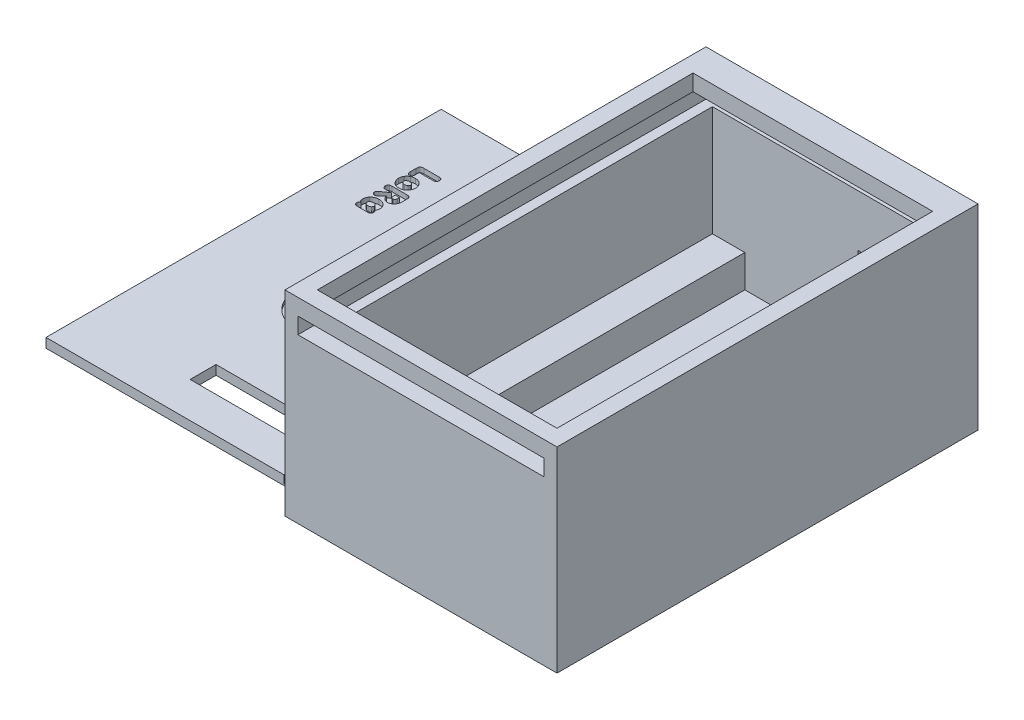
SolidWorks part; units mm, degrees
ref_plane "Plan de face" through (0, 0, 0) normal (0, 0, 1) x (1, 0, 0)
ref_plane "Plan de dessus" through (0, 0, 0) normal (0, 1, 0) x (1, 0, 0)
ref_plane "Plan de droite" through (0, 0, 0) normal (1, 0, 0) x (0, 0, -1)
sketch "Esquisse2" plane through (0, 0, 0) normal (0, 1, 0) x (1, 0, 0)
  line L1 (-71.4701, 44.7879) -> (-39.4701, 44.7879)
  line L2 (-71.4701, 44.7879) -> (-71.4701, -10.2121)
  line L3 (-71.4701, -10.2121) -> (-39.4701, -10.2121)
  line L4 (-39.4701, 44.7879) -> (-39.4701, -10.2121)
extrude "Boss.-Extru.1" add sketch "Esquisse2" along normal blind 3
sketch "Esquisse3" plane through (-71.4701, 0, 0) normal (-1, 0, 0) x (0, 0, 1)
  line L1 (-44.7879, 0) -> (10.2121, 0)
  line L2 (-44.7879, 0) -> (-44.7879, 30)
  line L3 (-44.7879, 30) -> (10.2121, 30)
  line L4 (10.2121, 0) -> (10.2121, 30)
extrude "Boss.-Extru.2" add sketch "Esquisse3" along normal blind 3
sketch "Esquisse5" plane through (-39.4701, 0, 0) normal (1, 0, 0) x (0, 0, -1)
  line L1 (-10.2121, 30) -> (44.7879, 30)
  line L2 (-10.2121, 30) -> (-10.2121, 0)
  line L3 (-10.2121, 0) -> (44.7879, 0)
  line L4 (44.7879, 30) -> (44.7879, 0)
extrude "Boss.-Extru.3" add sketch "Esquisse5" along normal blind 3
sketch "Esquisse6" plane through (0, 0, -44.7879) normal (0, 0, -1) x (-1, 0, 0)
  line L1 (36.4701, 30) -> (74.4701, 30)
  line L2 (36.4701, 30) -> (36.4701, 0)
  line L3 (36.4701, 0) -> (74.4701, 0)
  line L4 (74.4701, 30) -> (74.4701, 0)
extrude "Boss.-Extru.4" add sketch "Esquisse6" along normal blind 3
sketch "Esquisse7" plane through (0, 0, 10.2121) normal (0, 0, 1) x (1, 0, 0)
  line L1 (-74.4701, 30) -> (-36.4701, 30)
  line L2 (-74.4701, 30) -> (-74.4701, 0)
  line L3 (-74.4701, 0) -> (-36.4701, 0)
  line L4 (-36.4701, 30) -> (-36.4701, 0)
extrude "Boss.-Extru.5" add sketch "Esquisse7" along normal blind 3
sketch "Esquisse8" plane through (0, 3, 0) normal (0, 1, 0) x (1, 0, 0)
  line L0 (-39.4701, -10.2121) -> (-71.4701, -10.2121) construction
  line L1 (-71.4701, 44.7879) -> (-67.9701, 44.7879)
  line L2 (-71.4701, 44.7879) -> (-71.4701, -10.2121)
  line L3 (-71.4701, -10.2121) -> (-67.9701, -10.2121)
  line L4 (-67.9701, 44.7879) -> (-67.9701, -10.2121)
extrude "Boss.-Extru.6" add sketch "Esquisse8" along normal blind 5
sketch "Esquisse9" plane through (0, 3, 0) normal (0, 1, 0) x (1, 0, 0)
  line L0 (-67.9701, -10.2121) -> (-39.4701, -10.2121) construction
  line L1 (-39.4701, 44.7879) -> (-42.9701, 44.7879)
  line L2 (-39.4701, 44.7879) -> (-39.4701, -10.2121)
  line L3 (-39.4701, -10.2121) -> (-42.9701, -10.2121)
  line L4 (-42.9701, 44.7879) -> (-42.9701, -10.2121)
extrude "Boss.-Extru.7" add sketch "Esquisse9" along normal blind 5
sketch "Esquisse12" plane through (0, 0, 10.2121) normal (0, 0, -1) x (-1, 0, 0)
  line L0 (39.4701, 30) -> (39.4701, 8) construction
  line L1 (71.4701, 8) -> (71.4701, 30) construction
  line L2 (39.4701, 27.5) -> (71.4701, 27.5)
  line L3 (39.4701, 27.5) -> (39.4701, 25)
  line L4 (39.4701, 25) -> (71.4701, 25)
  line L5 (71.4701, 27.5) -> (71.4701, 25)
  point P0 (39.4701, 25)
  point P1 (39.4701, 27.5)
  dimension "D1" = 5
  dimension "D2" = 2.5
extrude "Enlèv. mat.-Extru.1" cut sketch "Esquisse12" against normal through all
sketch "Esquisse13" plane through (0, 0, -47.7879) normal (0, 0, -1) x (-1, 0, 0)
  line L1 (36.4701, 30) -> (74.4701, 30)
  line L2 (36.4701, 30) -> (36.4701, 0)
  line L3 (36.4701, 0) -> (74.4701, 0)
  line L4 (74.4701, 30) -> (74.4701, 0)
extrude "Boss.-Extru.8" add sketch "Esquisse13" along normal blind 2
sketch "Esquisse14" plane through (-36.4701, 0, 0) normal (1, 0, 0) x (0, 0, -1)
  line L1 (-13.2121, 30) -> (49.7879, 30)
  line L2 (-13.2121, 30) -> (-13.2121, 0)
  line L3 (-13.2121, 0) -> (49.7879, 0)
  line L4 (49.7879, 30) -> (49.7879, 0)
extrude "Boss.-Extru.9" add sketch "Esquisse14" along normal blind 2
sketch "Esquisse15" plane through (0, 0, 13.2121) normal (0, 0, 1) x (1, 0, 0)
  line L1 (-74.4701, 30) -> (-34.4701, 30)
  line L2 (-74.4701, 30) -> (-74.4701, 0)
  line L3 (-74.4701, 0) -> (-34.4701, 0)
  line L4 (-34.4701, 30) -> (-34.4701, 0)
extrude "Boss.-Extru.10" add sketch "Esquisse15" along normal blind 2
sketch "Esquisse16" plane through (0, 0, 13.2121) normal (0, 0, -1) x (-1, 0, 0)
  line L0 (71.4701, 25) -> (71.4701, 27.5) construction
  line L1 (39.4701, 25) -> (71.4701, 25)
  line L2 (39.4701, 25) -> (39.4701, 27.5)
  line L3 (39.4701, 27.5) -> (71.4701, 27.5)
  line L4 (71.4701, 25) -> (71.4701, 27.5)
extrude "Enlèv. mat.-Extru.2" cut sketch "Esquisse16" against normal blind 2
sketch "Esquisse17" plane through (-74.4701, 0, 0) normal (-1, 0, 0) x (0, 0, 1)
  line L1 (-49.7879, 30) -> (15.2121, 30)
  line L2 (-49.7879, 30) -> (-49.7879, 0)
  line L3 (-49.7879, 0) -> (15.2121, 0)
  line L4 (15.2121, 30) -> (15.2121, 0)
extrude "Boss.-Extru.11" add sketch "Esquisse17" along normal blind 2
sketch "Esquisse18" plane through (-39.4701, 0, 0) normal (-1, 0, 0) x (0, 0, 1)
  line L0 (-44.7879, 8) -> (-44.7879, 30) construction
  line L1 (15.2121, 27.5) -> (-44.7879, 27.5)
  line L2 (15.2121, 27.5) -> (15.2121, 25)
  line L3 (15.2121, 25) -> (-44.7879, 25)
  line L4 (-44.7879, 27.5) -> (-44.7879, 25)
extrude "Enlèv. mat.-Extru.3" cut sketch "Esquisse18" against normal blind 3
sketch "Esquisse19" plane through (-71.4701, 0, 0) normal (1, 0, 0) x (0, 0, -1)
  line L0 (44.7879, 30) -> (44.7879, 8) construction
  line L1 (-15.2121, 27.5) -> (44.7879, 27.5)
  line L2 (-15.2121, 27.5) -> (-15.2121, 25)
  line L3 (-15.2121, 25) -> (44.7879, 25)
  line L4 (44.7879, 27.5) -> (44.7879, 25)
extrude "Enlèv. mat.-Extru.4" cut sketch "Esquisse19" against normal blind 3
sketch "Esquisse20" plane through (0, 0, -44.7879) normal (0, 0, 1) x (1, 0, 0)
  line L1 (-74.4701, 27.5) -> (-36.4701, 27.5)
  line L2 (-74.4701, 27.5) -> (-74.4701, 25)
  line L3 (-74.4701, 25) -> (-36.4701, 25)
  line L4 (-36.4701, 27.5) -> (-36.4701, 25)
extrude "Enlèv. mat.-Extru.5" cut sketch "Esquisse20" against normal blind 3
sketch "Esquisse22" plane through (0, 0, 0) normal (0, -1, 0) x (1, 0, 0)
  line L1 (-76.4701, 15.2121) -> (-80.6146, 15.2121)
  line L2 (-76.4701, 15.2121) -> (-76.4701, -49.7879)
  line L3 (-76.4701, -49.7879) -> (-80.6146, -49.7879)
  line L4 (-80.6146, 15.2121) -> (-80.6146, -49.7879)
extrude "Boss.-Extru.12" add sketch "Esquisse22" along normal blind 0.5 separate body
sketch "Esquisse23" plane through (-80.6146, 0, 0) normal (-1, 0, 0) x (0, 0, 1)
  line L0 (15.2121, 0) -> (15.2121, 30) construction
  line L1 (-49.7879, -0.5) -> (15.2121, -0.5)
  line L2 (-49.7879, -0.5) -> (-49.7879, 1.95)
  line L3 (-49.7879, 1.95) -> (15.2121, 1.95)
  line L4 (15.2121, -0.5) -> (15.2121, 1.95)
extrude "Boss.-Extru.13" add sketch "Esquisse23" along normal blind 37.5
sketch "Esquisse24" plane through (0, 0, 15.2121) normal (0, 0, 1) x (1, 0, 0)
  line L0 (-76.4701, -0.5) -> (-118.1146, -0.5) construction
  line L1 (-118.1146, 1.95) -> (-80.6146, 1.95)
  line L2 (-118.1146, 1.95) -> (-118.1146, -0.5)
  line L3 (-118.1146, -0.5) -> (-80.6146, -0.5)
  line L4 (-80.6146, 1.95) -> (-80.6146, -0.5)
extrude "Enlèv. mat.-Extru.6" cut sketch "Esquisse24" against normal blind 2
sketch "Esquisse25" plane through (0, 0, 0) normal (0, 1, 0) x (1, 0, 0)
  line L0 (-76.4701, 49.7879) -> (-76.4701, -15.2121) construction
  line L1 (-80.6146, -15.2121) -> (-76.4701, -15.2121)
  line L2 (-80.6146, -15.2121) -> (-80.6146, -13.2121)
  line L3 (-80.6146, -13.2121) -> (-76.4701, -13.2121)
  line L4 (-76.4701, -15.2121) -> (-76.4701, -13.2121)
extrude "Enlèv. mat.-Extru.7" cut sketch "Esquisse25" against normal through all
sketch "Esquisse26" plane through (0, 0, 0) normal (0, -1, 0) x (1, 0, 0)
  line L1 (-76.4701, -49.7879) -> (-34.4701, -49.7879)
  line L2 (-76.4701, -49.7879) -> (-76.4701, 15.2121)
  line L3 (-76.4701, 15.2121) -> (-34.4701, 15.2121)
  line L4 (-34.4701, -49.7879) -> (-34.4701, 15.2121)
extrude "Boss.-Extru.14" add sketch "Esquisse26" along normal through all
sketch "Esquisse29" plane through (0, 0, 10.2121) normal (0, 0, -1) x (-1, 0, 0)
  line L1 (42.9701, 8) -> (67.9701, 8)
  line L2 (42.9701, 8) -> (42.9701, 3)
  line L3 (42.9701, 3) -> (67.9701, 3)
  line L4 (67.9701, 8) -> (67.9701, 3)
extrude "Boss.-Extru.16" add sketch "Esquisse29" along normal blind 3.5
sketch "Esquisse31" plane through (-42.9701, 0, 0) normal (-1, 0, 0) x (0, 0, 1)
  line L0 (-44.7879, 3) -> (6.7121, 3) construction
  line L1 (-44.7879, 8) -> (-42.2879, 8)
  line L2 (-44.7879, 8) -> (-44.7879, 3)
  line L3 (-44.7879, 3) -> (-42.2879, 3)
  line L4 (-42.2879, 8) -> (-42.2879, 3)
extrude "Enlèv. mat.-Extru.8" cut sketch "Esquisse31" against normal blind 3.5
sketch "Esquisse32" plane through (0, 0, -44.7879) normal (0, 0, 1) x (1, 0, 0)
  line L0 (-67.9701, 8) -> (-39.4701, 8)
  line L1 (-39.4701, 3) -> (-39.4701, 25) construction
  line L2 (-50.4701, 8) -> (-50.4701, 19)
  point P5 (-50.4701, 8)
  dimension "D1" = 11
sketch "Esquisse33" plane through (0, 0, -44.7879) normal (0, 0, 1) x (1, 0, 0)
  line L1 (-50.4701, 19) -> (-39.4701, 19)
  line L2 (-50.4701, 19) -> (-50.4701, 8)
  line L3 (-50.4701, 8) -> (-39.4701, 8)
  line L4 (-39.4701, 19) -> (-39.4701, 8)
extrude "Enlèv. mat.-Extru.10" cut sketch "Esquisse33" against normal through all
sketch "Esquisse34" plane through (0, 1.95, 0) normal (0, 1, 0) x (1, 0, 0)
  line L1 (-80.6146, -13.2121) -> (-80.6146, 49.7879) construction
  line L3 (-80.6146, -5.7081) -> (-80.6146, -1.7081)
  line L5 (-80.6146, -5.7081) -> (-100.6146, -5.7081)
  line L7 (-80.6146, -1.7081) -> (-100.6146, -1.7081)
  line L8 (-100.6146, -5.7081) -> (-100.6146, -1.7081)
extrude "Enlèv. mat.-Extru.12" cut sketch "Esquisse34" against normal through all
sketch "Esquisse36" plane through (-2.0057, 1.95, -1.3008) normal (0, 1, 0) x (1, 0, 0)
  circle A0 centre (-97.3476, 12.9377) radius 5
extrude "Enlèv. mat.-Extru.13" cut sketch "Esquisse36" against normal blind 1.2
sketch "Esquisse37" plane through (0, 1.95, 0) normal (0, 1, 0) x (1, 0, 0)
  line L0 (-118.1146, 14.2428) -> (-80.6146, 14.2428)
  line L1 (-118.1146, -13.2121) -> (-118.1146, 49.7879) construction
  line L2 (-80.6146, -1.7081) -> (-80.6146, 49.7879) construction
  point P6 (-99.3646, 14.2428)
sketch "Esquisse38" plane through (0, 0, 10.2121) normal (0, 0, -1) x (-1, 0, 0)
  line L1 (39.4701, 30) -> (71.4701, 30)
  line L2 (39.4701, 30) -> (39.4701, 8)
  line L3 (39.4701, 8) -> (71.4701, 8)
  line L4 (71.4701, 30) -> (71.4701, 8)
extrude "Enlèv. mat.-Extru.14" cut sketch "Esquisse38" against normal blind 2.5
sketch "Esquisse40" plane through (0, 0, -44.7879) normal (0, 0, 1) x (1, 0, 0)
  line L0 (-39.4701, 3) -> (-39.4701, 8) construction
  line L1 (-71.4701, 30) -> (-39.4701, 30)
  line L2 (-71.4701, 30) -> (-71.4701, 3)
  line L3 (-71.4701, 3) -> (-39.4701, 3)
  line L4 (-39.4701, 30) -> (-39.4701, 3)
extrude "Enlèv. mat.-Extru.15" cut sketch "Esquisse40" against normal blind 2.5
sketch "Esquisse42" plane through (-71.4701, 0, 0) normal (1, 0, 0) x (0, 0, -1)
  line L0 (47.2879, 25) -> (47.2879, 3) construction
  line L1 (-12.7121, 30) -> (47.2879, 30)
  line L2 (-12.7121, 30) -> (-12.7121, 8)
  line L3 (-12.7121, 8) -> (47.2879, 8)
  line L4 (47.2879, 30) -> (47.2879, 8)
extrude "Enlèv. mat.-Extru.16" cut sketch "Esquisse42" against normal blind 2.5
sketch "Esquisse43" plane through (-39.4701, 0, 0) normal (-1, 0, 0) x (0, 0, 1)
  line L1 (-47.2879, 30) -> (12.7121, 30)
  line L2 (-47.2879, 30) -> (-47.2879, 8)
  line L3 (-47.2879, 8) -> (12.7121, 8)
  line L4 (12.7121, 30) -> (12.7121, 8)
extrude "Enlèv. mat.-Extru.17" cut sketch "Esquisse43" against normal blind 2.5
sketch "Esquisse44" plane through (0, 0, -42.2879) normal (0, 0, -1) x (-1, 0, 0)
  line L1 (39.4701, 8) -> (42.9701, 8)
  line L2 (39.4701, 8) -> (39.4701, 3)
  line L3 (39.4701, 3) -> (42.9701, 3)
  line L4 (42.9701, 8) -> (42.9701, 3)
extrude "Enlèv. mat.-Extru.18" cut sketch "Esquisse44" against normal blind 5
sketch "Esquisse45" plane through (-39.4701, 0, 0) normal (-1, 0, 0) x (0, 0, 1)
  line L0 (-37.2879, 8) -> (-37.2879, 3) construction
  line L1 (-47.2879, 8) -> (-37.2879, 8)
  line L2 (-47.2879, 8) -> (-47.2879, 3)
  line L3 (-47.2879, 3) -> (-37.2879, 3)
  line L4 (-37.2879, 8) -> (-37.2879, 3)
  line L5 (-47.2879, 3) -> (-37.2879, 3) construction
extrude "Enlèv. mat.-Extru.19" cut sketch "Esquisse45" against normal blind 2.5
sketch "Esquisse47" plane through (-118.1146, 0, 0) normal (-1, 0, 0) x (0, 0, 1)
  line L0 (13.2121, 1.95) -> (13.2121, -0.5) construction
  line L1 (-49.7879, 1.95) -> (13.2121, 1.95)
  line L2 (-49.7879, 1.95) -> (-49.7879, -0.5)
  line L3 (-49.7879, -0.5) -> (13.2121, -0.5)
  line L4 (13.2121, 1.95) -> (13.2121, -0.5)
  line L5 (-49.7879, -0.5) -> (13.2121, -0.5) construction
extrude "Enlèv. mat.-Extru.20" cut sketch "Esquisse47" against normal blind 2
sketch "Esquisse48" plane through (0, 0, 13.2121) normal (0, 0, 1) x (1, 0, 0)
  line L1 (-116.1146, 1.95) -> (-76.4701, 1.95)
  line L2 (-116.1146, 1.95) -> (-116.1146, -0.5)
  line L3 (-116.1146, -0.5) -> (-76.4701, -0.5)
  line L4 (-76.4701, 1.95) -> (-76.4701, -0.5)
extrude "Enlèv. mat.-Extru.21" cut sketch "Esquisse48" against normal blind 2
sketch "Esquisse49" plane through (0, -0.5, 0) normal (0, -1, 0) x (1, 0, 0)
  line L1 (-34.4701, 15.2121) -> (-116.1146, 15.2121)
  line L2 (-34.4701, 15.2121) -> (-34.4701, -49.7879)
  line L3 (-34.4701, -49.7879) -> (-116.1146, -49.7879)
  line L4 (-116.1146, 15.2121) -> (-116.1146, -49.7879)
extrude "Enlèv. mat.-Extru.23" cut sketch "Esquisse49" against normal blind 0.25
sketch "Esquisse50" plane through (0, 1.95, 0) normal (0, 1, 0) x (1, 0, 0)
  line L1 (-116.1146, 49.7879) -> (-80.6146, 49.7879)
  line L2 (-116.1146, 49.7879) -> (-116.1146, -11.2121)
  line L3 (-116.1146, -11.2121) -> (-80.6146, -11.2121)
  line L4 (-80.6146, 49.7879) -> (-80.6146, -11.2121)
extrude "Enlèv. mat.-Extru.24" cut sketch "Esquisse50" against normal blind 0.75
sketch "Esquisse53" plane through (-39.4701, 0, 0) normal (-1, 0, 0) x (0, 0, 1)
  line L0 (-49.7879, 8) -> (-49.7879, 19) construction
  line L1 (-47.2879, 8) -> (-49.7879, 8)
  line L2 (-47.2879, 8) -> (-47.2879, 19)
  line L3 (-47.2879, 19) -> (-49.7879, 19)
  line L4 (-49.7879, 8) -> (-49.7879, 19)
extrude "Boss.-Extru.17" add sketch "Esquisse53" along normal blind 1.5
sketch "Esquisse54" plane through (0, 19, 0) normal (0, -1, 0) x (1, 0, 0)
  line L1 (-50.4701, -49.7879) -> (-40.9701, -49.7879)
  line L2 (-50.4701, -49.7879) -> (-50.4701, -47.2879)
  line L3 (-50.4701, -47.2879) -> (-40.9701, -47.2879)
  line L4 (-40.9701, -49.7879) -> (-40.9701, -47.2879)
extrude "Boss.-Extru.19" add sketch "Esquisse54" along normal blind 2
sketch "Esquisse55" plane through (-36.9701, 0, 0) normal (-1, 0, 0) x (0, 0, 1)
  line L1 (-47.2879, 25) -> (12.7121, 25)
  line L2 (-47.2879, 25) -> (-47.2879, 3)
  line L3 (-47.2879, 3) -> (12.7121, 3)
  line L4 (12.7121, 25) -> (12.7121, 3)
extrude "Boss.-Extru.20" add sketch "Esquisse55" along normal blind 1
sketch "Esquisse56" plane through (-73.9701, 0, 0) normal (1, 0, 0) x (0, 0, -1)
  line L0 (-12.7121, 8) -> (47.2879, 8) construction
  line L1 (-12.7121, 25) -> (47.2879, 25)
  line L2 (-12.7121, 25) -> (-12.7121, 8)
  line L3 (-12.7121, 8) -> (47.2879, 8)
  line L4 (47.2879, 25) -> (47.2879, 8)
extrude "Boss.-Extru.21" add sketch "Esquisse56" along normal blind 1
sketch "Esquisse57" plane through (-71.4701, 0, 0) normal (1, 0, 0) x (0, 0, -1)
  line L1 (44.7879, 8) -> (47.2879, 8)
  line L2 (44.7879, 8) -> (44.7879, 3)
  line L3 (44.7879, 3) -> (47.2879, 3)
  line L4 (47.2879, 8) -> (47.2879, 3)
extrude "Boss.-Extru.22" add sketch "Esquisse57" along normal blind 3.5
sketch "Esquisse58" plane through (0, 0, -47.2879) normal (0, 0, 1) x (1, 0, 0)
  line L0 (-73.9701, 27.5) -> (-36.9701, 27.5) construction
  line L1 (-73.9701, 30) -> (-36.9701, 30)
  line L2 (-73.9701, 30) -> (-73.9701, 27.5)
  line L3 (-73.9701, 27.5) -> (-36.9701, 27.5)
  line L4 (-36.9701, 30) -> (-36.9701, 27.5)
extrude "Boss.-Extru.23" add sketch "Esquisse58" along normal blind 2
sketch "Esquisse59" plane through (-116.1146, 0, 0) normal (-1, 0, 0) x (0, 0, 1)
  line L1 (-49.7879, 1.2) -> (11.2121, 1.2)
  line L2 (-49.7879, 1.2) -> (-49.7879, -0.25)
  line L3 (-49.7879, -0.25) -> (11.2121, -0.25)
  line L4 (11.2121, 1.2) -> (11.2121, -0.25)
extrude "Boss.-Extru.24" add sketch "Esquisse59" along normal blind 1.25
sketch "Esquisse62" plane through (0, 1.2, 0) normal (0, 1, 0) x (1, 0, 0)
  text T0 "<b>LoRa</b>" font "VAG Rundschrift D" height 3.5
extrude "Enlèv. mat.-Extru.27" cut sketch "Esquisse62" against normal blind 0.75
